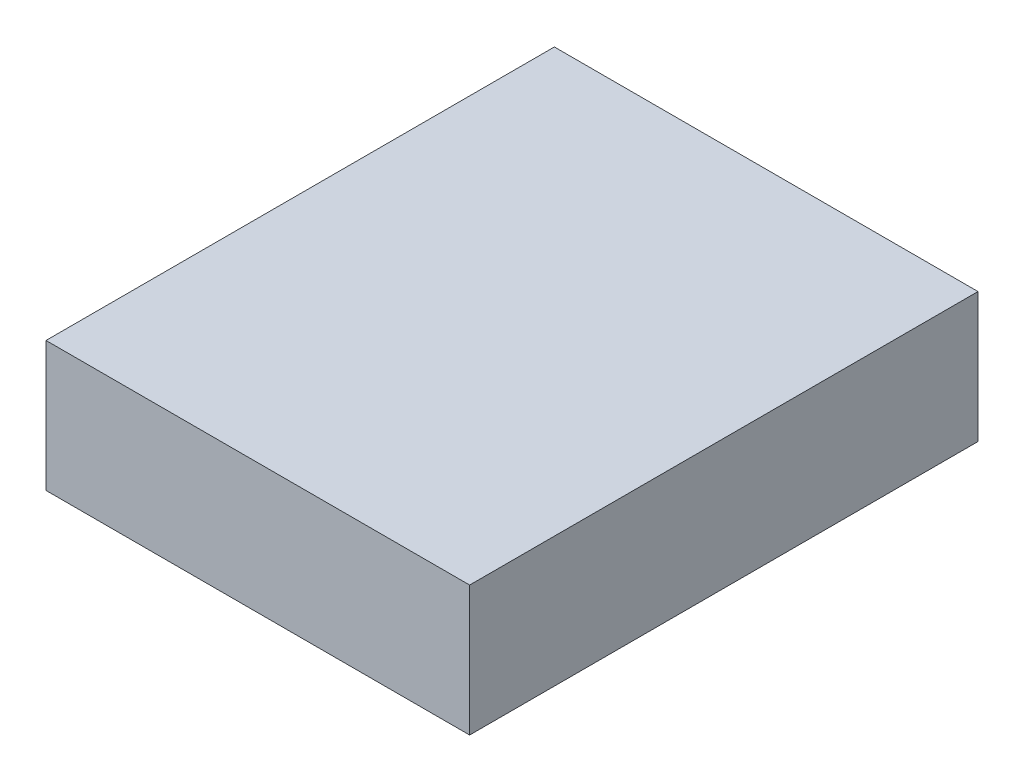
SolidWorks part; units mm, degrees
ref_plane "Front Plane" through (0, 0, 0) normal (0, 0, 1) x (1, 0, 0)
ref_plane "Top Plane" through (0, 0, 0) normal (0, 1, 0) x (1, 0, 0)
ref_plane "Right Plane" through (0, 0, 0) normal (1, 0, 0) x (0, 0, -1)
sketch "Sketch1" plane through (0, 0, 0) normal (0, 1, 0) x (1, 0, 0)
  line L1 (-37.5627, 26.2685) -> (1462.4373, 26.2685)
  line L2 (-37.5627, 26.2685) -> (-37.5627, -1773.7315)
  line L3 (-37.5627, -1773.7315) -> (1462.4373, -1773.7315)
  line L4 (1462.4373, 26.2685) -> (1462.4373, -1773.7315)
  dimension "D1" = 1500
  dimension "D2" = 1800
extrude "Boss-Extrude1" add sketch "Sketch1" along normal blind 460
